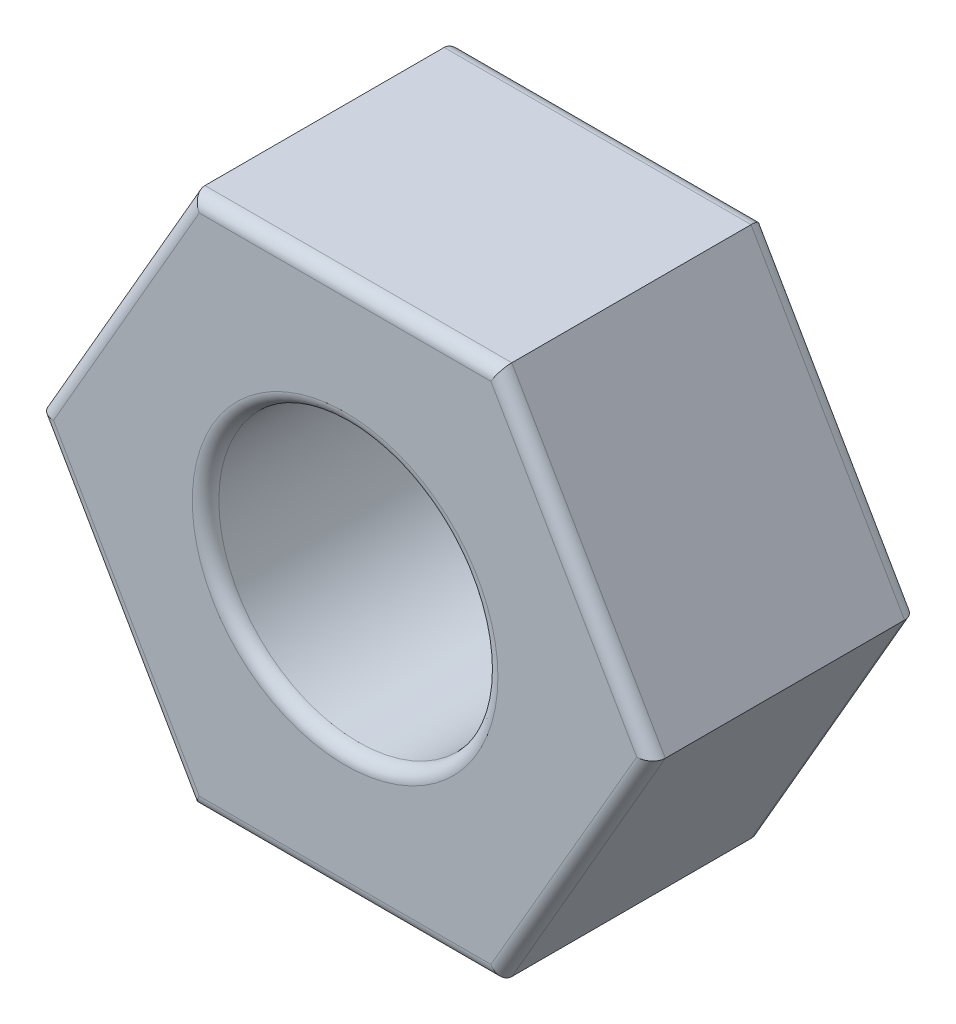
SolidWorks part; units mm, degrees
ref_plane "Front Plane" through (0, 0, 0) normal (0, 0, 1) x (1, 0, 0)
ref_plane "Top Plane" through (0, 0, 0) normal (0, 1, 0) x (1, 0, 0)
ref_plane "Right Plane" through (0, 0, 0) normal (1, 0, 0) x (0, 0, -1)
sketch "Sketch1" plane through (0, 0, 0) normal (0, 0, 1) x (1, 0, 0)
  line L1 (4.6188, 0) -> (2.3094, 4)
  line L2 (2.3094, 4) -> (-2.3094, 4)
  line L3 (-2.3094, 4) -> (-4.6188, 0)
  line L4 (-4.6188, 0) -> (-2.3094, -4)
  line L5 (-2.3094, -4) -> (2.3094, -4)
  line L6 (2.3094, -4) -> (4.6188, 0)
  circle A0 centre (0, 0) radius 4 construction
  circle A1 centre (0, 0) radius 2.1
  dimension "D1" = 8
  dimension "D2" = 4.2
extrude "Boss-Extrude1" add sketch "Sketch1" along normal blind 4
fillet "Fillet1" radius 0.2 14 edges at (2.1, 0, 4) (0, -4, 4) (-3.4641, -2, 4) (-3.4641, 2, 4) (0, 4, 4) (3.4641, 2, 4) (3.4641, -2, 4) (2.1, 0, 0) (3.4641, 2, 0) (0, 4, 0) (-3.4641, 2, 0) (-3.4641, -2, 0) (0, -4, 0) (3.4641, -2, 0)
